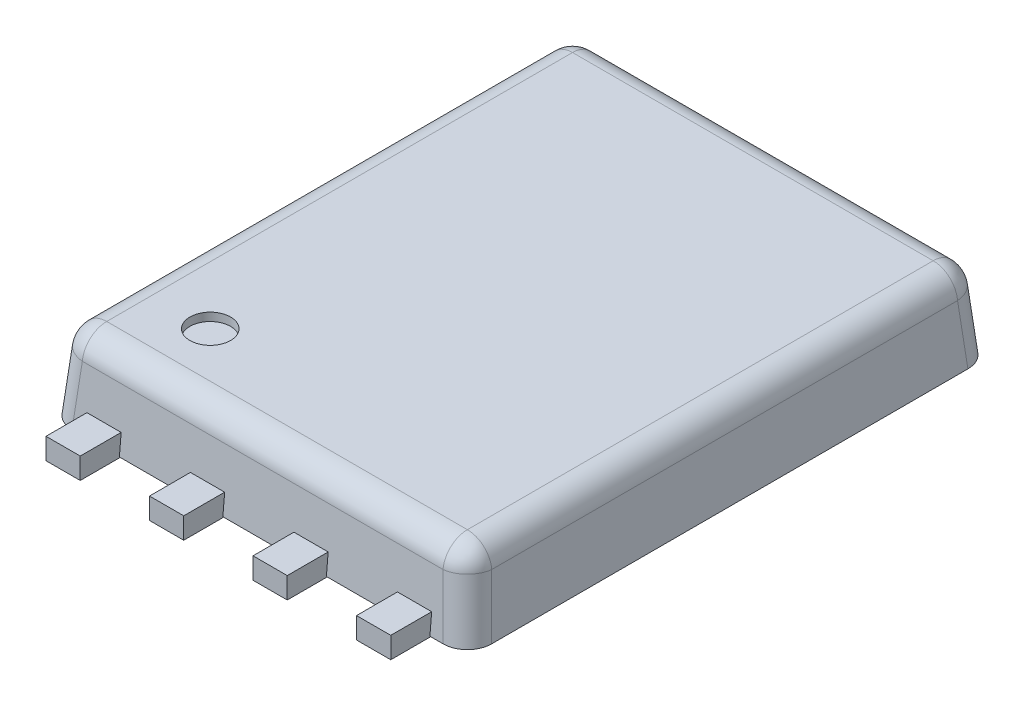
SolidWorks part; units mm, degrees
ref_plane "Спереди" through (0, 0, 0) normal (0, 0, 1) x (1, 0, 0)
ref_plane "Сверху" through (0, 0, 0) normal (0, 1, 0) x (1, 0, 0)
ref_plane "Справа" through (0, 0, 0) normal (1, 0, 0) x (0, 0, -1)
sketch "Эскиз1" plane through (0, 0, 0) normal (0, 1, 0) x (1, 0, 0)
  line L1 (-2.575, 3.22) -> (2.575, 3.22)
  line L2 (-2.575, 3.22) -> (-2.575, -3.22)
  line L3 (-2.575, -3.22) -> (2.575, -3.22)
  line L4 (2.575, 3.22) -> (2.575, -3.22)
  line L5 (-2.575, 3.22) -> (2.575, -3.22) construction
  line L6 (-2.575, -3.22) -> (2.575, 3.22) construction
  point P0 (0, 0)
  dimension "D1" = 6.44
  dimension "D2" = 5.15
extrude "Бобышка-Вытянуть1" add sketch "Эскиз1" along normal blind 1 draft 5
fillet "Скругление1" radius 0.3 8 edges at (0, 1, 3.1325) (-2.4875, 1, 0) (0, 1, -3.1325) (2.4875, 1, 0) (-2.5313, 0.5, -3.1763) (2.5313, 0.5, -3.1763) (2.5313, 0.5, 3.1763) (-2.5313, 0.5, 3.1763)
sketch "Эскиз2" plane through (0, 1, 0) normal (0, 1, 0) x (1, 0, 0)
  circle A0 centre (-1.5, -2.3) radius 0.25
  point P2 (0, 0)
  dimension "D1" = 0.5
  dimension "D2" = 1.5
  dimension "D3" = 2.3
extrude "Вырез-Вытянуть1" cut sketch "Эскиз2" against normal blind 0.1
sketch "Эскиз3" plane through (0, 0, 0) normal (0, -1, 0) x (1, 0, 0)
  line L0 (-1000, 0) -> (49000, 0) construction
  line L1 (0, -1000) -> (0, 49000) construction
  line L2 (-0.425, 2.7902) -> (-0.425, 3.7002)
  line L3 (2.115, 2.7902) -> (1.695, 2.7902)
  line L4 (2.115, 2.7902) -> (2.115, 3.7002)
  line L5 (2.115, 3.7002) -> (1.695, 3.7002)
  line L6 (1.695, 2.7902) -> (1.695, 3.7002)
  line L7 (0.845, 2.7902) -> (0.425, 2.7902)
  line L8 (0.845, 2.7902) -> (0.845, 3.7002)
  line L9 (0.845, 3.7002) -> (0.425, 3.7002)
  line L10 (0.425, 2.7902) -> (0.425, 3.7002)
  line L11 (-0.845, 3.7002) -> (-0.425, 3.7002)
  line L12 (-0.845, 2.7902) -> (-0.845, 3.7002)
  line L13 (-0.845, 2.7902) -> (-0.425, 2.7902)
  line L14 (-1.695, 2.7902) -> (-1.695, 3.7002)
  line L15 (-2.115, 3.7002) -> (-1.695, 3.7002)
  line L16 (-2.115, 2.7902) -> (-2.115, 3.7002)
  line L17 (-2.115, 2.7902) -> (-1.695, 2.7902)
  point P21 (-0.635, 3.7002)
  point P22 (0.635, 3.7002)
  point P23 (1.905, 3.7002)
  point P24 (-1.905, 3.7002)
  dimension "D1" = 0.91
  dimension "D2" = 0.42
  dimension "D3" = 1.27
  dimension "D4" = 3.81
extrude "Бобышка-Вытянуть2" add sketch "Эскиз3" against normal blind 0.25 and the other way blind 0.01
